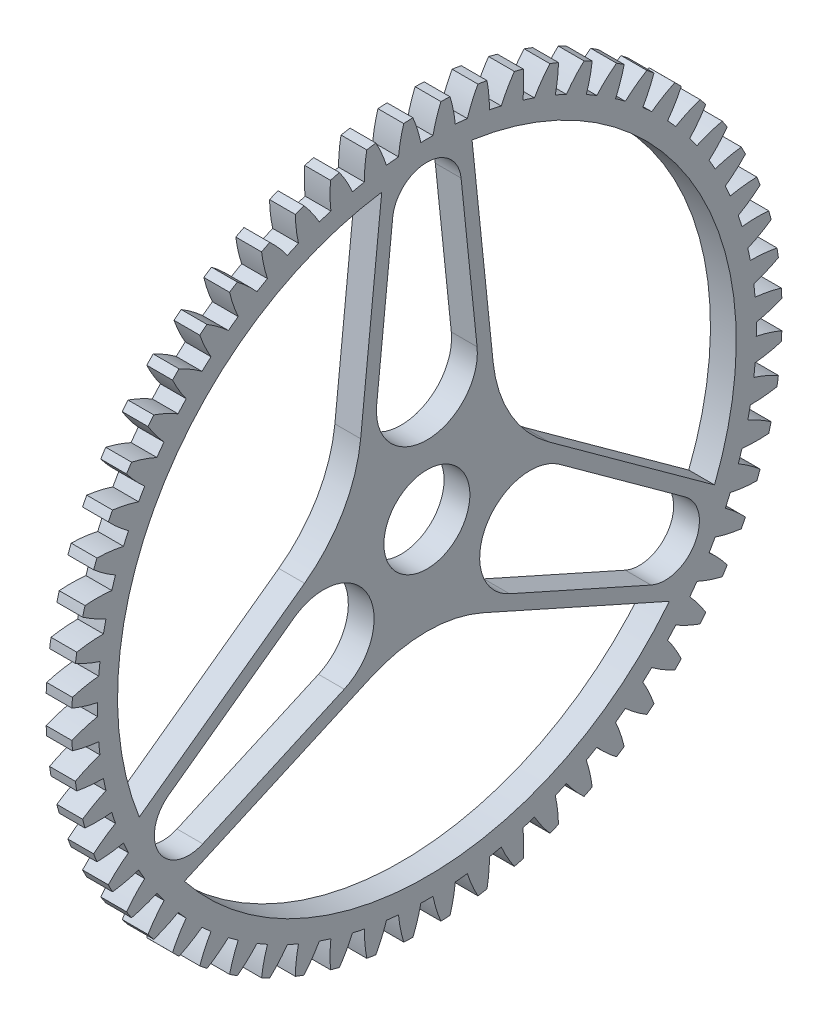
SolidWorks part; units mm, degrees
material "PVC 0.007 Plasticized"
ref_plane "Plane1" through (0, 0, 0) normal (0, 0, 1) x (1, 0, 0)
ref_plane "Plane2" through (0, 0, 0) normal (0, 1, 0) x (1, 0, 0)
ref_plane "Plane3" through (0, 0, 0) normal (1, 0, 0) x (0, 0, -1)
other "Configuration Table"
sketch "HoldingSke" plane through (0, 0, 0) normal (0, 1, 0) x (1, 0, 0)
  line L0 (0, 0) -> (152.4, -263.9645)
  line L1 (-15, 0) -> (100, 0) construction
  line L2 (0, 0) -> (-2.1039, 2.3779)
  line L3 (0, 0) -> (-11.863, 4.5341)
  line L4 (0, 0) -> (4.318, 7.479)
  line L5 (0, 0) -> (-47.5972, -17.7524)
  line L6 (0, 0) -> (-3.9479, -2.6637)
  line L7 (-2.1039, 2.3779) -> (8.8308, 51.9871)
  line L8 (-76.2, 54.61) -> (-58.1914, 54.61)
  line L9 (-67.7845, 28.3722) -> (-49.3413, 33.142)
  line L10 (-76.2, 71.12) -> (104.1128, 71.12)
  line L11 (0, 0) -> (-4.7625, 0)
  line L12 (-76.2, 101.6) -> (-76.1147, 101.6)
  line L13 (24.9733, 27.94) -> (52.9518, 28.4284)
  line L14 (24.9733, 27.94) -> (24.9746, 27.94)
  line L15 (24.9733, 27.94) -> (100.4006, 29.5858)
  circle A0 centre (0, 0) radius 7.9375
  circle A1 centre (0, 0) radius 38.1
  circle A2 centre (0, 0) radius 38.1
  circle A3 centre (0, 0) radius 7.9375
  dimension "MHD" = 76.2
  dimension "Hub_dia" = 76.2
  dimension "Bore" = 15.875
  dimension "MBD" = 15.875
  dimension "Num_teeth" = 60
  dimension "Pitch" = 304.8
  dimension "Overall_len" = 50.8
  dimension "Show_teeth" = 60
  dimension "Thickness" = 4.7625
  dimension "OAL" = 50.8001
  dimension "T_dim" = 18.0086
  dimension "Ap" = 14.5
  dimension "H" = 19.05
  dimension "Pitch_radius" = 180.3128
  dimension "Width" = 4.7625
  dimension "Backlash" = 0.0853
  dimension "Addendum_fac" = 1
  dimension "Dedendum_fac" = 1.25
  dimension "Clearance_fac" = 0.25
  dimension "Dedendum_add" = 0.0013
sketch "BasProSke" plane through (0, 0, 0) normal (0, 1, 0) x (1, 0, 0)
  line L0 (-10, 0) -> (60, 0) construction
  line L1 (0, 0) -> (0, 65.6167)
  line L2 (0, 0) -> (4.7625, 0)
  line L3 (4.7625, 0) -> (4.7625, 65.6167)
  line L4 (4.7625, 65.6167) -> (0, 65.6167)
  dimension "Thickness" = 4.7625
  dimension "Diameter" = 131.2333
revolve "Base-Revolve" add sketch "BasProSke" angle 360 about L0
sketch "TooCutSke" plane through (0, 0, 0) normal (1, 0, 0) x (0, 0, -1)
  line L1 (0, 0) -> (0, 107) construction
  line L2 (0, 0) -> (-1.8116, 63.4742) construction
  line L3 (0, 0) -> (-6.6448, 126.79) construction
  line L4 (-1.8116, 63.4742) -> (-3.3224, 63.395) construction
  arc A0 (1.1199, 60.8426) -> (-1.1199, 60.8426) centre (0, 0) ccw
  arc A1 (2.5964, 65.5907) -> (-2.5964, 65.5907) centre (0, 0) ccw
  circle A2 centre (0, 0) radius 63.5 construction
  circle A3 centre (0, 0) radius 61.4774 construction
  arc A4 (-1.1199, 60.8426) -> (-2.5964, 65.5907) centre (-25.996, 55.7106) ccw
  arc A5 (2.5964, 65.5907) -> (1.1199, 60.8426) centre (25.996, 55.7106) ccw
  dimension "Root_dia" = 121.7058
  dimension "Overcut_dia" = 131.2841
  dimension "Pitch_dia" = 127
  dimension "Base_dia" = 122.9548
  dimension "Flank_rad" = 25.4
  dimension "Half_ang" = 3
  dimension "Half_CT" = 1.5129
extrude "ToothCut" cut sketch "TooCutSke" along normal through all
fillet "Breaks" [suppressed] radius 0.0423
fillet "RootFillets" [suppressed] radius 0.5304
pattern_circular "TeethCuts" count 60 every 6 about axis through (-10, 0, 0) along (1, 0, 0) of "ToothCut", "RootFillets", "Breaks"
sketch "HubNeaOneSke" plane through (0, 0, 0) normal (-1, 0, 0) x (0, 0, 1)
  circle A0 centre (0, 0) radius 38.1
  dimension "Diameter" = 76.2
extrude "HubNearOne" [suppressed] add sketch "HubNeaOneSke" along normal blind 46.0376
sketch "HubNeaBotSke" plane through (0, 0, 0) normal (-1, 0, 0) x (0, 0, 1)
  circle A0 centre (0, 0) radius 38.1
  dimension "Diameter" = 76.2
extrude "HubNearBoth" [suppressed] add sketch "HubNeaBotSke" along normal blind 23.0188
ref_plane "FarPln" through (4.7625, 0, 0) normal (1, 0, 0) x (0, 0, -1)
sketch "HubFarSke" plane through (4.7625, 0, 0) normal (1, 0, 0) x (0, 0, -1)
  circle A0 centre (0, 0) radius 38.1
  dimension "Diameter" = 76.2
extrude "HubFar" [suppressed] add sketch "HubFarSke" along normal blind 23.0188
sketch "BorSke" plane through (0, 0, 0) normal (1, 0, 0) x (0, 0, -1)
  circle A0 centre (0, 0) radius 7.9375
  dimension "Diameter" = 15.875
extrude "Bore" cut sketch "BorSke" along normal mid plane 101.6001
sketch "KeySke" plane through (0, 0, 0) normal (1, 0, 0) x (0, 0, -1)
  line L0 (-2.3813, 0) -> (-2.3813, 10.0711)
  line L1 (-2.3813, 10.0711) -> (2.3813, 10.0711)
  line L2 (2.3813, 10.0711) -> (2.3813, 0)
  line L3 (0, 0) -> (0, 34) construction
  line L4 (-2.3813, 0) -> (2.3813, 0)
  dimension "Width" = 4.7625
  dimension "Offset" = 10.0711
extrude "Keyway" [suppressed] cut sketch "KeySke" along normal mid plane 101.6001
pattern_circular "Keyway2" [suppressed] count 2 every 90 about axis through (-10, 0, 0) along (1, 0, 0)
sketch "Sketch1" plane through (4.7625, 0, 0) normal (1, 0, 0) x (0, 0, -1)
  line L0 (0, 0) -> (0, 60.8529) construction
  line L1 (0, 0) -> (52.7002, 30.4264) construction
  line L2 (0, 0) -> (52.7002, -30.4264) construction
  line L3 (0, 0) -> (0, -60.8529) construction
  line L4 (0, 0) -> (-52.7002, -30.4264) construction
  line L5 (0, 0) -> (-52.7002, 30.4264) construction
  line L6 (-10.9985, 6.35) -> (-6.3161, 51.4557)
  line L7 (10.9985, 6.35) -> (6.3161, 51.4557)
  line L8 (10.9985, 6.35) -> (47.72, -20.258)
  line L9 (0, -12.7) -> (41.4039, -31.1977)
  line L10 (0, -12.7) -> (-41.4039, -31.1977)
  line L11 (-10.9985, 6.35) -> (-47.72, -20.258)
  line L12 (-13.4078, 7.741) -> (-8.8425, 51.7179)
  line L13 (13.4078, 7.741) -> (8.8425, 51.7179)
  line L14 (13.4078, 7.741) -> (49.2103, -18.2012)
  line L15 (0, -15.482) -> (40.3678, -33.5168)
  line L16 (0, -15.482) -> (-40.3678, -33.5168)
  line L17 (-13.4078, 7.741) -> (-49.2103, -18.2012)
  line L18 (-8.8425, 51.7179) -> (-8.3421, 56.5379)
  line L19 (8.8425, 51.7179) -> (8.3421, 56.5379)
  line L20 (49.2103, -18.2012) -> (53.1343, -21.0445)
  line L21 (40.3678, -33.5168) -> (44.7922, -35.4934)
  line L22 (-49.2103, -18.2012) -> (-53.1343, -21.0445)
  line L23 (-40.3678, -33.5168) -> (-44.7922, -35.4934)
  circle A0 centre (0, 0) radius 60.8529 construction
  arc A1 (-8.3421, 56.5379) -> (-53.1343, -21.0445) centre (0, 0) ccw
  circle A2 centre (0, 0) radius 12.7
  circle A4 centre (0, 0) radius 50.8 construction
  arc A5 (6.3161, 51.4557) -> (-6.3161, 51.4557) centre (0, 50.8) ccw
  arc A6 (41.4039, -31.1977) -> (47.72, -20.258) centre (43.9941, -25.4) ccw
  arc A7 (-47.72, -20.258) -> (-41.4039, -31.1977) centre (-43.9941, -25.4) ccw
  arc A12 (8.8425, 51.7179) -> (-8.8425, 51.7179) centre (0, 50.8) ccw construction
  arc A13 (53.1343, -21.0445) -> (8.3421, 56.5379) centre (0, 0) ccw
  arc A15 (40.3678, -33.5168) -> (49.2103, -18.2012) centre (43.9941, -25.4) ccw construction
  arc A16 (-44.7922, -35.4934) -> (44.7922, -35.4934) centre (0, 0) ccw
  arc A18 (-49.2103, -18.2012) -> (-40.3678, -33.5168) centre (-43.9941, -25.4) ccw construction
  arc A19 (-9.2717, 22.9841) -> (9.2717, 22.9841) centre (0, 22.0216) ccw
  arc A20 (24.5406, -3.4625) -> (15.2689, -19.5216) centre (19.0712, -11.0108) ccw
  arc A21 (-15.2689, -19.5216) -> (-24.5406, -3.4625) centre (-19.0712, -11.0108) ccw
  circle A22 centre (0, 0) radius 22.0216 construction
  point P13 (0, 0)
  point P14 (0, 0)
  dimension "D1" = 25.4
  dimension "D3" = 114.3
  dimension "D4" = 101.6
  dimension "D5" = 2.54
  dimension "D2" = 6
extrude "Cut-Extrude7" cut sketch "Sketch1" against normal through all
fillet "Fillet1" radius 25.4 3 edges at (2.3813, 7.741, 13.4078) (2.3813, -15.482, 0) (2.3813, 7.741, -13.4078)
equation "' \"Pitch@HoldingSke\" = 4"
equation "' \"Num_teeth@HoldingSke\" = 12"
equation "' \"Ap@HoldingSke\" =  20"
equation "' \"Ap@HoldingSke\" = 20"
equation "' \"Width@HoldingSke\" = 0.5"
equation "' \"Hub_dia@HoldingSke\"= 1"
equation "' \"Hub_dia@HoldingSke\" = 1"
equation "' \"Overall_len@HoldingSke\" = 1.0"
equation "' \"Bore@HoldingSke\" = 0.75"
equation "' \"T_dim@HoldingSke\" = 0.85"
equation "' \"Width@KeySke\" = 0.25"
equation "' \"Show_teeth@HoldingSke\" = 13"
equation "' \"Backlash@HoldingSke\" = 0.009"
equation "' \"Addendum_fac@HoldingSke\" = 1.0"
equation "' \"Dedendum_fac@HoldingSke\" = 1.25"
equation "' \"Dedendum_add@HoldingSke\" = 0.00005"
equation "' \"Clearance_fac@HoldingSke\" = 0.25"
equation "' \"Pitch@HoldingSke\" = 0.5"
equation "' \"Num_teeth@HoldingSke\" = 23"
equation "' \"Show_teeth@HoldingSke\" = 23"
equation "' \"Backlash@HoldingSke\" = 0.0375"
equation "\"Overcut_dia@TooCutSke\" = (\"Num_teeth@HoldingSke\" + 2 * \"Addendum_fac@HoldingSke\") / \"Pitch@HoldingSke\" + 0.002"
equation "\"Pitch_dia@TooCutSke\" = \"Num_teeth@HoldingSke\" / \"Pitch@HoldingSke\""
equation "\"Base_dia@TooCutSke\" = \"Num_teeth@HoldingSke\" / \"Pitch@HoldingSke\" * cos((\"Ap@HoldingSke\"  * 3.14159265 / 180))"
equation "\"Root_dia@TooCutSke\" = (\"Num_teeth@HoldingSke\" + 2) / \"Pitch@HoldingSke\" - 2 * (\"Addendum_fac@HoldingSke\" + \"Dedendum_fac@HoldingSke\") / \"Pitch@HoldingSke\" - \"Dedendum_add@HoldingSke\" * 2"
equation "\"Half_ang@TooCutSke\" = 180 / \"Num_teeth@HoldingSke\""
equation "\"Half_CT@TooCutSke\" = \"Num_teeth@HoldingSke\" / \"Pitch@HoldingSke\" * sin((3.14159265 / 2 / \"Num_teeth@HoldingSke\")) / 2 - 7 * \"Backlash@HoldingSke\" / 4"
equation "\"Flank_rad@TooCutSke\" = \"Num_teeth@HoldingSke\" / \"Pitch@HoldingSke\" / 5"
equation "\"Radius@RootFillets\" = \"Clearance_fac@HoldingSke\" / \"Pitch@HoldingSke\" + \"Dedendum_add@HoldingSke\""
equation "\"Break_rad@Breaks\" = 0.02 / \"Pitch@HoldingSke\""
equation "\"Thickness@HoldingSke\" = \"Width@HoldingSke\""
equation "\"OAL@HoldingSke\" = \"Thickness@HoldingSke\""
equation "\"MHD@HoldingSke\" = (\"Num_teeth@HoldingSke\" + 2) / \"Pitch@HoldingSke\" - 2 * (\"Addendum_fac@HoldingSke\" + \"Dedendum_fac@HoldingSke\")  / \"Pitch@HoldingSke\" - \"Dedendum_add@HoldingSke\" * 2"
equation "\"MBD@HoldingSke\" = (\"Num_teeth@HoldingSke\" + 2) / \"Pitch@HoldingSke\" - 2 * (\"Addendum_fac@HoldingSke\" + \"Dedendum_fac@HoldingSke\")  / \"Pitch@HoldingSke\" - \"Dedendum_add@HoldingSke\" * 2 - 0.002"
equation "\"MHD@HoldingSke\" = ((sgn( \"MHD@HoldingSke\" - \"Hub_dia@HoldingSke\" )-1)*( \"MHD@HoldingSke\" - \"Hub_dia@HoldingSke\" ))/-2+ \"Hub_dia@HoldingSke\""
equation "\"MBD@HoldingSke\" = ((sgn( \"MBD@HoldingSke\" - \"Bore@HoldingSke\" )-1)*( \"MBD@HoldingSke\" - \"Bore@HoldingSke\" ))/-2+ \"Bore@HoldingSke\""
equation "\"OAL@HoldingSke\" = ((sgn( \"OAL@HoldingSke\" - \"Overall_len@HoldingSke\" )+1)*( \"OAL@HoldingSke\" - \"Overall_len@HoldingSke\" ))/2 + \"Overall_len@HoldingSke\" + 0.000002"
equation "\"Num_teeth@TeethCuts\" = int( \"Show_teeth@HoldingSke\" ) + 1"
equation "\"Num_teeth@TeethCuts\" = ((sgn( \"Num_teeth@TeethCuts\" - \"Num_teeth@HoldingSke\" )-1)*( \"Num_teeth@TeethCuts\" - \"Num_teeth@HoldingSke\" ))/-2+ \"Num_teeth@HoldingSke\""
equation "\"Num_teeth@TeethCuts\" = ((sgn( \"Num_teeth@TeethCuts\" - 2.0)+1)*( \"Num_teeth@TeethCuts\" - 2.0))/2 +2.0"
equation "\"Angle@TeethCuts\" = 360.0 / \"Num_teeth@HoldingSke\""
equation "\"Diameter@BasProSke\" = (\"Num_teeth@HoldingSke\" + 2 * \"Addendum_fac@HoldingSke\") / \"Pitch@HoldingSke\""
equation "\"Thickness@BasProSke\"  = \"Thickness@HoldingSke\""
equation "' \"Fillet_rad@BasProSke\" =  \"Thickness@HoldingSke\" * 0.05"
equation "' \"Fillet_rad@BasProSke\" = \"Thickness@HoldingSke\" * 0.05"
equation "\"MHD@HoldingSke\" = ((sgn( \"MHD@HoldingSke\" - \"Root_dia@TooCutSke\" )-1)*( \"MHD@HoldingSke\" - \"Root_dia@TooCutSke\" ))/-2+ \"Root_dia@TooCutSke\""
equation "\"Diameter@HubNeaOneSke\" = \"MHD@HoldingSke\""
equation "\"Length@HubNearOne\" = \"OAL@HoldingSke\" - \"Thickness@BasProSke\""
equation "\"Diameter@HubNeaBotSke\" = \"MHD@HoldingSke\""
equation "\"Length@HubNearBoth\" = ( \"OAL@HoldingSke\" - \"Thickness@BasProSke\" ) / 2.0"
equation "\"Thickness@FarPln\" = \"Thickness@BasProSke\""
equation "\"Diameter@HubFarSke\" = \"MHD@HoldingSke\""
equation "\"Length@HubFar\" = ( \"OAL@HoldingSke\" - \"Thickness@BasProSke\" ) / 2.0"
equation "\"Diameter@BorSke\" = \"MBD@HoldingSke\""
equation "\"D1@Bore\" = \"OAL@HoldingSke\" * 2.0"
equation "\"D1@Keyway\" = \"OAL@HoldingSke\" * 2.0"
equation "\"Offset@KeySke\" = \"T_dim@HoldingSke\" - \"MBD@HoldingSke\" / 2.0"
